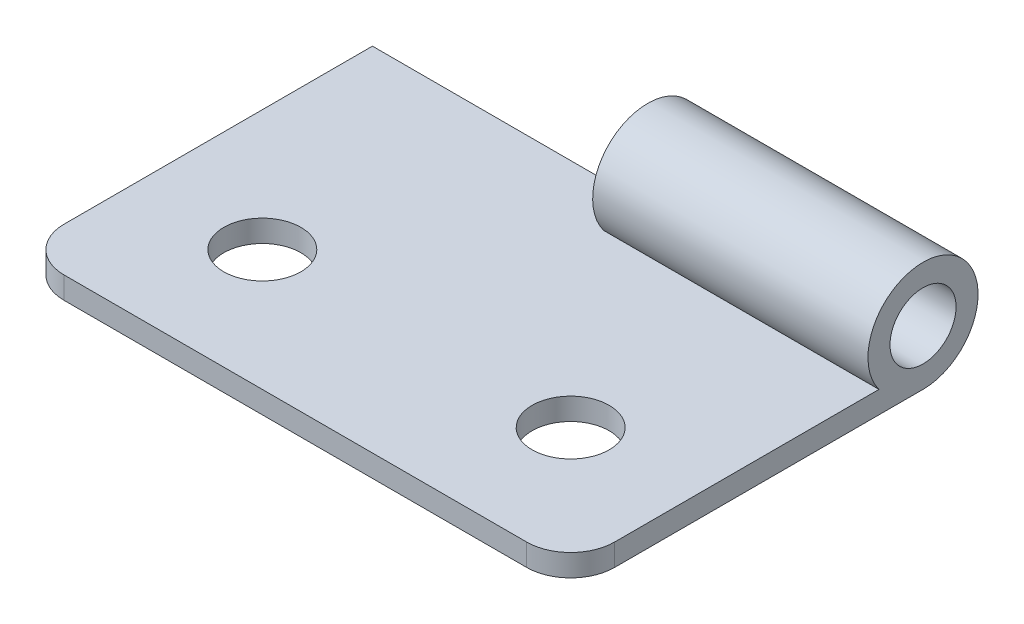
SolidWorks part; units mm, degrees
ref_plane "前视基准面" through (0, 0, 0) normal (0, 0, 1) x (1, 0, 0)
ref_plane "上视基准面" through (0, 0, 0) normal (0, 1, 0) x (1, 0, 0)
ref_plane "右视基准面" through (0, 0, 0) normal (1, 0, 0) x (0, 0, -1)
sketch "草图1" plane through (0, 0, 0) normal (0, 1, 0) x (1, 0, 0)
  line L1 (-12.5, 8) -> (12.5, 8)
  line L2 (-12.5, 8) -> (-12.5, -8)
  line L3 (-12.5, -8) -> (12.5, -8)
  line L4 (12.5, 8) -> (12.5, -8)
  line L5 (-12.5, 8) -> (12.5, -8) construction
  line L6 (-12.5, -8) -> (12.5, 8) construction
  point P0 (0, 0)
  dimension "D1" = 25
  dimension "D2" = 16
extrude "凸台-拉伸1" add sketch "草图1" along normal blind 1
sketch "草图2" plane through (0, 1, 0) normal (0, 1, 0) x (1, 0, 0)
  line L0 (-7, -2.5) -> (7, -2.5) construction
  line L1 (-12.5, -8) -> (12.5, -8) construction
  line L2 (12.5, 8) -> (-12.5, 8) construction
  circle A0 centre (-7, -2.5) radius 1.75
  circle A1 centre (7, -2.5) radius 1.75
  point P3 (0, -2.5)
  dimension "D3" = 3.5
  dimension "D1" = 10.5
  dimension "D2" = 14
extrude "切除-拉伸1" cut sketch "草图2" against normal through all
sketch "草图3" plane through (12.5, 0, 0) normal (1, 0, 0) x (0, 0, -1)
  circle A0 centre (8, 2.5) radius 2.5
  circle A1 centre (8, 2.5) radius 1.5
  dimension "D1" = 5
extrude "凸台-拉伸2" add sketch "草图3" against normal blind 12.5
fillet "圆角1" radius 2 2 edges at (12.5, 0.5, 8) (-12.5, 0.5, 8)
